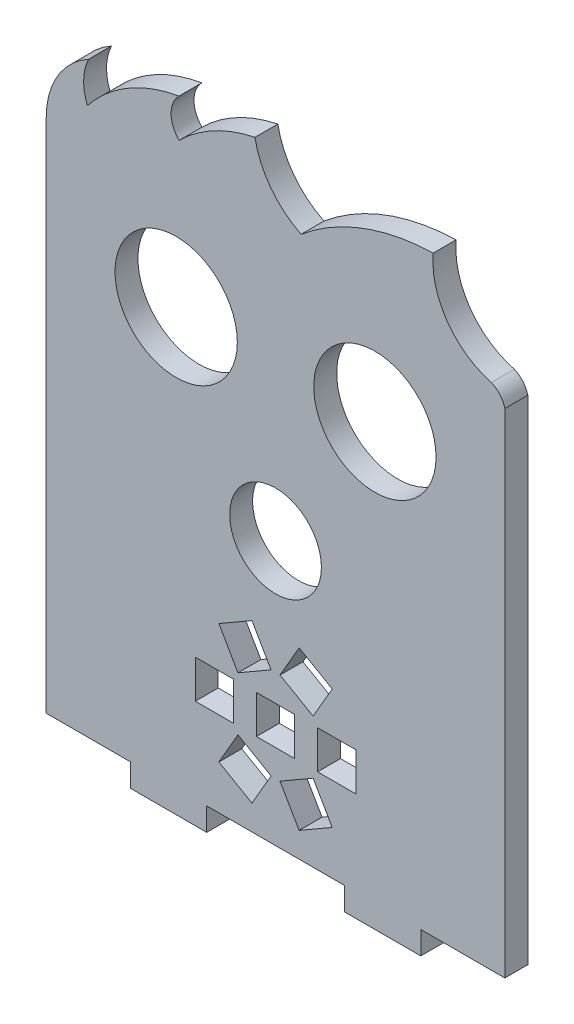
SolidWorks part; units mm, degrees
ref_plane "Alzado" through (0, 0, 0) normal (0, 0, 1) x (1, 0, 0)
ref_plane "Planta" through (0, 0, 0) normal (0, 1, 0) x (1, 0, 0)
ref_plane "Vista lateral" through (0, 0, 0) normal (1, 0, 0) x (0, 0, -1)
sketch "Model" plane through (0, 0, 0) normal (0, 0, 1) x (1, 0, 0)
  line L0 (61.2136, -33.6819) -> (61.2136, -30.6819)
  line L1 (61.2136, -30.6819) -> (72.2136, -30.6819)
  line L2 (72.2136, -30.6819) -> (72.2136, 33.8432)
  line L3 (47.1287, -13.5597) -> (49.6287, -9.2296)
  line L4 (49.6287, -9.2296) -> (45.2986, -6.7296)
  line L5 (45.2986, -6.7296) -> (42.7986, -11.0597)
  line L6 (42.7986, -11.0597) -> (47.1287, -13.5597)
  line L7 (34.7986, -9.2296) -> (37.2986, -13.5597)
  line L8 (37.2986, -13.5597) -> (41.6287, -11.0597)
  line L9 (41.6287, -11.0597) -> (39.1287, -6.7296)
  line L10 (39.1287, -6.7296) -> (34.7986, -9.2296)
  line L11 (52.7136, -14.5728) -> (47.7136, -14.5728)
  line L12 (47.7136, -14.5728) -> (47.7136, -19.5728)
  line L13 (47.7136, -19.5728) -> (52.7136, -19.5728)
  line L14 (52.7136, -19.5728) -> (52.7136, -14.5728)
  line L15 (44.7136, -14.5728) -> (39.7136, -14.5728)
  line L16 (39.7136, -14.5728) -> (39.7136, -19.5728)
  line L17 (39.7136, -19.5728) -> (44.7136, -19.5728)
  line L18 (44.7136, -19.5728) -> (44.7136, -14.5728)
  line L19 (49.6287, -24.9161) -> (47.1287, -20.586)
  line L20 (47.1287, -20.586) -> (42.7986, -23.086)
  line L21 (42.7986, -23.086) -> (45.2986, -27.4161)
  line L22 (45.2986, -27.4161) -> (49.6287, -24.9161)
  line L23 (36.7136, -14.5728) -> (31.7136, -14.5728)
  line L24 (31.7136, -14.5728) -> (31.7136, -19.5728)
  line L25 (31.7136, -19.5728) -> (36.7136, -19.5728)
  line L26 (36.7136, -19.5728) -> (36.7136, -14.5728)
  line L27 (37.2986, -20.586) -> (34.7986, -24.9161)
  line L28 (34.7986, -24.9161) -> (39.1287, -27.4161)
  line L29 (39.1287, -27.4161) -> (41.6287, -23.086)
  line L30 (41.6287, -23.086) -> (37.2986, -20.586)
  line L31 (33.2136, -33.6819) -> (33.2136, -30.6819)
  line L32 (33.2136, -30.6819) -> (51.2136, -30.6819)
  line L33 (51.2136, -30.6819) -> (51.2136, -33.6819)
  line L34 (23.2136, -30.6819) -> (23.2136, -33.6819)
  line L35 (12.2136, -30.6819) -> (23.2136, -30.6819)
  line L36 (12.2136, 36.8432) -> (12.2136, -30.6819)
  line L37 (61.2136, -33.6819) -> (51.2136, -33.6819)
  line L38 (33.2136, -33.6819) -> (23.2136, -33.6819)
  circle A0 centre (55.2136, 23.8432) radius 8
  circle A1 centre (29.2136, 23.8432) radius 8
  circle A2 centre (42.2136, 3.8432) radius 6
  arc A3 (72.2136, 33.8432) -> (70.4552, 35.9104) centre (69.2964, 33.1432) ccw
  arc A4 (62.8364, 46.7611) -> (70.4552, 35.9104) centre (73.1057, 45.8715) ccw
  arc A5 (62.8364, 46.7611) -> (45.5558, 40.2533) centre (63.4865, 18.8377) ccw
  arc A6 (39.519, 48.2256) -> (45.5558, 40.2533) centre (50.5097, 50.2762) ccw
  arc A7 (39.519, 48.2256) -> (29.5934, 42.9156) centre (43.5115, 28.8309) ccw
  arc A8 (29.5704, 47.9156) -> (29.5934, 42.9156) centre (32.0819, 45.4271) ccw
  arc A9 (29.5704, 47.9156) -> (17.6028, 40.8603) centre (32.7584, 28.8301) ccw
  arc A10 (17.7498, 46.183) -> (17.6028, 40.8603) centre (23.6248, 43.3574) ccw
  arc A11 (17.7498, 46.183) -> (12.2136, 36.8432) centre (22.8583, 36.8443) ccw
extrude "Saliente-Extruir1" add sketch "Model" along normal blind 3
